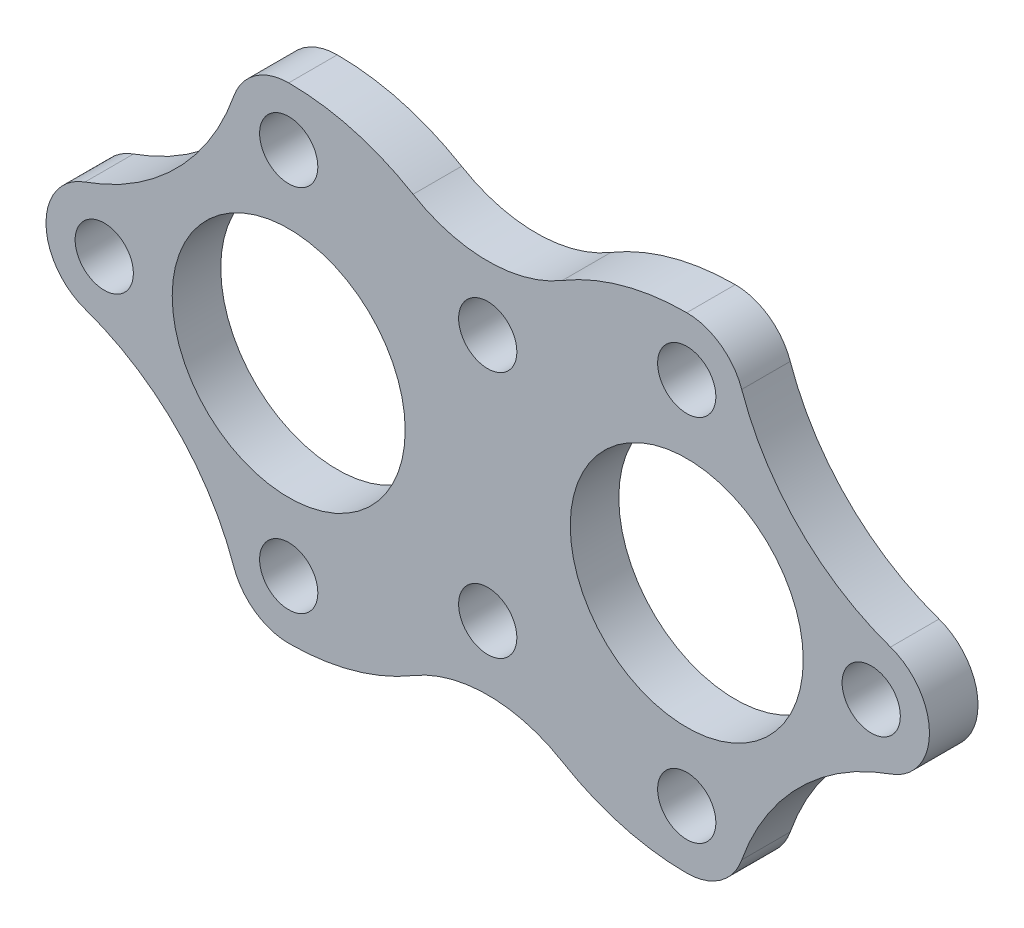
SolidWorks part; units mm, degrees
ref_plane "Спереди" through (0, 0, 0) normal (0, 0, 1) x (1, 0, 0)
ref_plane "Сверху" through (0, 0, 0) normal (0, 1, 0) x (1, 0, 0)
ref_plane "Справа" through (0, 0, 0) normal (1, 0, 0) x (0, 0, -1)
sketch "Эскиз1" plane through (0, 0, 0) normal (0, 0, 1) x (1, 0, 0)
  line L0 (0, -89.3939) -> (0, 89.3939) construction
  line L1 (-144.5063, 0) -> (144.5063, 0) construction
  circle A0 centre (41, 0) radius 24
  circle A1 centre (41, 0) radius 38 construction
  circle A2 centre (79, 0) radius 6
  circle A3 centre (41, -38) radius 6
  circle A4 centre (3, 0) radius 6 [skipped]
  circle A5 centre (41, 38) radius 6
  circle A6 centre (0, 25.5) radius 6
  circle A7 centre (0, -25.5) radius 6
  arc A9 (-15.375, 42.9344) -> (15.375, 42.9344) centre (0, 68.695) ccw
  arc A10 (52.3244, 41.9696) -> (82.9696, 11.3244) centre (99.5095, 58.5095) ccw
  arc A11 (52.3244, 41.9696) -> (41, 50) centre (41, 38) ccw
  arc A12 (41, 50) -> (15.375, 42.9344) centre (41, 0) ccw
  arc A13 (82.9696, -11.3244) -> (82.9696, 11.3244) centre (79, 0) ccw
  arc A14 (52.3244, -41.9696) -> (82.9696, -11.3244) centre (99.5095, -58.5095) cw
  arc A15 (52.3244, -41.9696) -> (41, -50) centre (41, -38) cw
  arc A16 (41, -50) -> (15.375, -42.9344) centre (41, 0) cw
  arc A17 (-15.375, -42.9344) -> (15.375, -42.9344) centre (0, -68.695) cw
  circle A18 centre (-41, 0) radius 38 construction
  circle A19 centre (-41, 0) radius 24
  circle A20 centre (-41, -38) radius 6
  circle A21 centre (-79, 0) radius 6
  circle A22 centre (-41, 38) radius 6
  arc A23 (-41, -50) -> (-15.375, -42.9344) centre (-41, 0) ccw
  arc A24 (-52.3244, -41.9696) -> (-41, -50) centre (-41, -38) ccw
  arc A25 (-52.3244, -41.9696) -> (-82.9696, -11.3244) centre (-99.5095, -58.5095) ccw
  arc A26 (-82.9696, -11.3244) -> (-82.9696, 11.3244) centre (-79, 0) cw
  arc A27 (-52.3244, 41.9696) -> (-82.9696, 11.3244) centre (-99.5095, 58.5095) cw
  arc A28 (-52.3244, 41.9696) -> (-41, 50) centre (-41, 38) cw
  arc A29 (-41, 50) -> (-15.375, 42.9344) centre (-41, 0) cw
  point P19 (41, 0)
  dimension "D1" = 48
  dimension "D3" = 76
  dimension "D4" = 12
  dimension "D6" = 12
  dimension "D9" = 30
  dimension "D11" = 12
  dimension "D8" = 50
  dimension "D12" = 12
  dimension "D10" = 50
  dimension "D2" = 41
  dimension "D7" = 51
  dimension "D5" = 4
extrude "Бобышка-Вытянуть1" add sketch "Эскиз1" along normal blind 10 contours A29 A28 A27 A26 A25 A24 A23 A17 A16 A15 A14 A13 A10 A11 A12 A9 A21 A19 A0 A2 A3 A5 A6 A7 A20 A22
equation "\"D11@Эскиз1\"=\"r\""
equation "\"r\"= 12"
equation "\"D4@Эскиз1\"=\"r\""
equation "\"D6@Эскиз1\"=\"r\""
equation "\"D1@Эскиз1\"=\"r\"*4"
